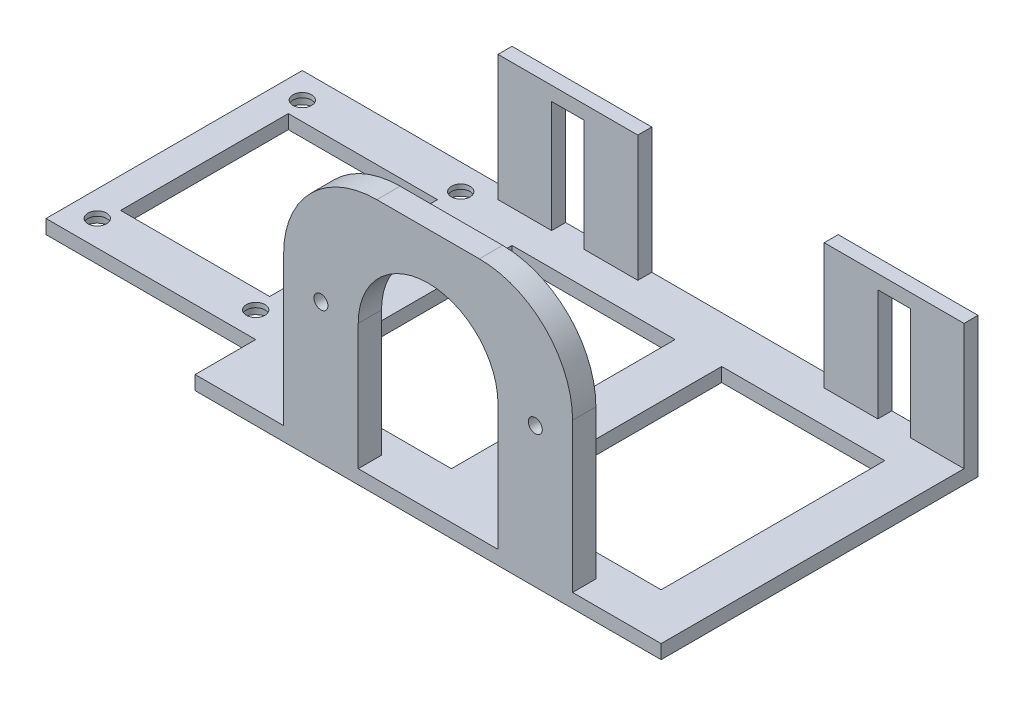
SolidWorks part; units mm, degrees
ref_plane "정면" through (0, 0, 0) normal (0, 0, 1) x (1, 0, 0)
ref_plane "윗면" through (0, 0, 0) normal (0, 1, 0) x (1, 0, 0)
ref_plane "우측면" through (0, 0, 0) normal (1, 0, 0) x (0, 0, -1)
sketch "스케치1" plane through (0, 0, 0) normal (0, 1, 0) x (1, 0, 0)
  line L1 (-50, 34) -> (50, 34)
  line L2 (-50, 34) -> (-50, -34)
  line L3 (-50, -34) -> (50, -34)
  line L4 (50, 34) -> (50, -34)
  line L5 (-50, 34) -> (50, -34) construction
  line L6 (-50, -34) -> (50, 34) construction
  point P0 (0, 0)
  dimension "D1" = 100
  dimension "D2" = 68
extrude "보스-돌출1" add sketch "스케치1" along normal blind 3
sketch "스케치2" plane through (0, 3, 0) normal (0, 1, 0) x (1, 0, 0)
  line L0 (-50, 34) -> (-50, -34) construction
  line L1 (50, 34) -> (-50, 34)
  line L2 (50, 34) -> (50, 31)
  line L3 (50, 31) -> (-50, 31)
  line L4 (-50, 34) -> (-50, 31)
  dimension "D1" = 3
extrude "보스-돌출2" add sketch "스케치2" along normal blind 27
sketch "스케치3" plane through (0, 0, -31) normal (0, 0, 1) x (1, 0, 0)
  line L0 (-50, 3) -> (50, 3) construction
  line L1 (-38.5, 27) -> (-31.5, 27)
  line L2 (-38.5, 27) -> (-38.5, 3)
  line L3 (-38.5, 3) -> (-31.5, 3)
  line L4 (-31.5, 27) -> (-31.5, 3)
  line L5 (-50, 30) -> (-50, 3) construction
  line L6 (-50, 3) -> (50, 3) construction
  line L7 (31.5, 27) -> (38.5, 27)
  line L8 (31.5, 27) -> (31.5, 3)
  line L9 (31.5, 3) -> (38.5, 3)
  line L10 (38.5, 27) -> (38.5, 3)
  line L11 (50, 30) -> (50, 3) construction
  dimension "D1" = 24
  dimension "D2" = 11.5
  dimension "D3" = 7
  dimension "D4" = 7
  dimension "D5" = 24
  dimension "D6" = 11.5
extrude "컷-돌출2" cut sketch "스케치3" against normal blind 27
sketch "스케치4" plane through (0, 3, 0) normal (0, 1, 0) x (1, 0, 0)
  line L0 (-50, -34) -> (50, -34) construction
  line L1 (-31, -29) -> (31, -29)
  line L2 (-31, -29) -> (-31, -34)
  line L3 (-31, -34) -> (31, -34)
  line L4 (31, -29) -> (31, -34)
  line L5 (50, -34) -> (50, 31) construction
  dimension "D1" = 5
  dimension "D2" = 62
  dimension "D3" = 19
extrude "보스-돌출3" add sketch "스케치4" along normal blind 52 contours L1 L4 L3 L2
sketch "스케치5" plane through (0, 0, 34) normal (0, 0, 1) x (1, 0, 0)
  line L0 (0, 55) -> (0, 0) construction
  line L1 (-50, 0) -> (50, 0) construction
  line L2 (-31, 55) -> (31, 55) construction
  line L3 (-15, 30) -> (-15, 3)
  line L4 (-15, 3) -> (15, 3)
  line L5 (15, 3) -> (15, 30)
  arc A0 (15, 30) -> (-15, 30) centre (0, 30) ccw
  circle A1 centre (-23, 30) radius 1.5
  circle A2 centre (23, 30) radius 1.5
  point P4 (0, 30)
  dimension "D2" = 15
  dimension "D4" = 3
  dimension "D7" = 23
  dimension "D8" = 3
  dimension "D1" = 30
  dimension "D3" = 3
  dimension "D5" = 23
  dimension "D6" = 30
extrude "컷-돌출4" cut sketch "스케치5" against normal blind 5
sketch "스케치7" plane through (0, 0, 0) normal (0, -1, 0) x (1, 0, 0)
  line L0 (50, 34) -> (50, -34) construction
  line L1 (40, 24) -> (5, 24)
  line L2 (40, 24) -> (40, -24)
  line L3 (40, -24) -> (5, -24)
  line L4 (5, 24) -> (5, -24)
  line L5 (50, -34) -> (-50, -34) construction
  line L6 (-50, 34) -> (50, 34) construction
  line L7 (-50, -34) -> (-50, 34) construction
  line L8 (-5, 24) -> (-40, 24)
  line L9 (-5, 24) -> (-5, -24)
  line L10 (-5, -24) -> (-40, -24)
  line L11 (-40, 24) -> (-40, -24)
  dimension "D1" = 10
  dimension "D2" = 10
  dimension "D3" = 10
  dimension "D4" = 10
  dimension "D5" = 10
  dimension "D6" = 10
  dimension "D7" = 5
  dimension "D8" = 5
extrude "컷-돌출5" cut sketch "스케치7" against normal blind 3
sketch "스케치11" plane through (-50, 0, 0) normal (-1, 0, 0) x (0, 0, 1)
  line L0 (-31, 3) -> (34, 3) construction
  line L1 (-34, 0) -> (21, 0)
  line L2 (-34, 0) -> (-34, 3)
  line L3 (-34, 3) -> (21, 3)
  line L4 (21, 0) -> (21, 3)
  dimension "D1" = 55
extrude "보스-돌출5" add sketch "스케치11" along normal blind 45
sketch "스케치13" plane through (0, 3, 0) normal (0, 1, 0) x (1, 0, 0)
  line L0 (-95, -21) -> (-50, -21) construction
  line L1 (-52.5, -18.5) -> (-92.5, -18.5) construction
  line L2 (-52.5, -18.5) -> (-52.5, 31.5) construction
  line L3 (-52.5, 31.5) -> (-92.5, 31.5) construction
  line L4 (-92.5, -18.5) -> (-92.5, 31.5) construction
  line L5 (-95, -21) -> (-95, 34) construction
  line L6 (-95, 34) -> (-50, 34) construction
  line L7 (-72.5, -18.5) -> (-72.5, 31.5) construction
  line L8 (-52.5, 6.5) -> (-92.5, 6.5) construction
  line L10 (-56.5, -11.5) -> (-88.5, -11.5)
  line L11 (-56.5, -11.5) -> (-56.5, 24.5)
  line L12 (-56.5, 24.5) -> (-88.5, 24.5)
  line L13 (-88.5, -11.5) -> (-88.5, 24.5)
  circle A0 centre (-55.5, -15.5) radius 2
  circle A1 centre (-89.5, -15.5) radius 2
  circle A2 centre (-89.5, 28.5) radius 2
  circle A3 centre (-55.5, 28.5) radius 2
  dimension "D5" = 4
  dimension "D6" = 3
  dimension "D7" = 3
  dimension "D8" = 4
  dimension "D9" = 4
  dimension "D1" = 2.5
  dimension "D2" = 2.5
  dimension "D3" = 2.5
  dimension "D4" = 40
  dimension "D10" = 7
  dimension "D11" = 7
extrude "컷-돌출8" cut sketch "스케치13" against normal blind 3
sketch "스케치14" plane through (0, 0, 0) normal (0, -1, 0) x (1, 0, 0)
  line L1 (-89.5, 15.5) -> (-55.5, 15.5) construction
  line L2 (-89.5, 15.5) -> (-89.5, -28.5) construction
  line L3 (-89.5, -28.5) -> (-55.5, -28.5) construction
  line L4 (-55.5, 15.5) -> (-55.5, -28.5) construction
  circle A0 centre (-89.5, 15.5) radius 3
  circle A1 centre (-89.5, -28.5) radius 3
  circle A2 centre (-55.5, -28.5) radius 3
  circle A3 centre (-55.5, 15.5) radius 3
  dimension "D1" = 6
  dimension "D2" = 6
  dimension "D3" = 6
  dimension "D4" = 6
extrude "컷-돌출9" cut sketch "스케치14" against normal blind 2
sketch "스케치15" plane through (0, 0, -34) normal (0, 0, -1) x (-1, 0, 0)
  line L0 (-50, 30) -> (50, 30) construction
  line L1 (-20, 30) -> (20, 30)
  line L2 (-20, 30) -> (-20, 3)
  line L3 (-20, 3) -> (20, 3)
  line L4 (20, 30) -> (20, 3)
  line L5 (-31.5, 27) -> (-31.5, 3) construction
  line L6 (31.5, 3) -> (31.5, 27) construction
  line L7 (-50, 0) -> (95, 0) construction
  dimension "D1" = 11.5
  dimension "D2" = 11.5
  dimension "D3" = 3
extrude "컷-돌출10" cut sketch "스케치15" against normal blind 3
fillet "필렛1" radius 20 2 edges at (31, 55, 31.5) (-31, 55, 31.5)
